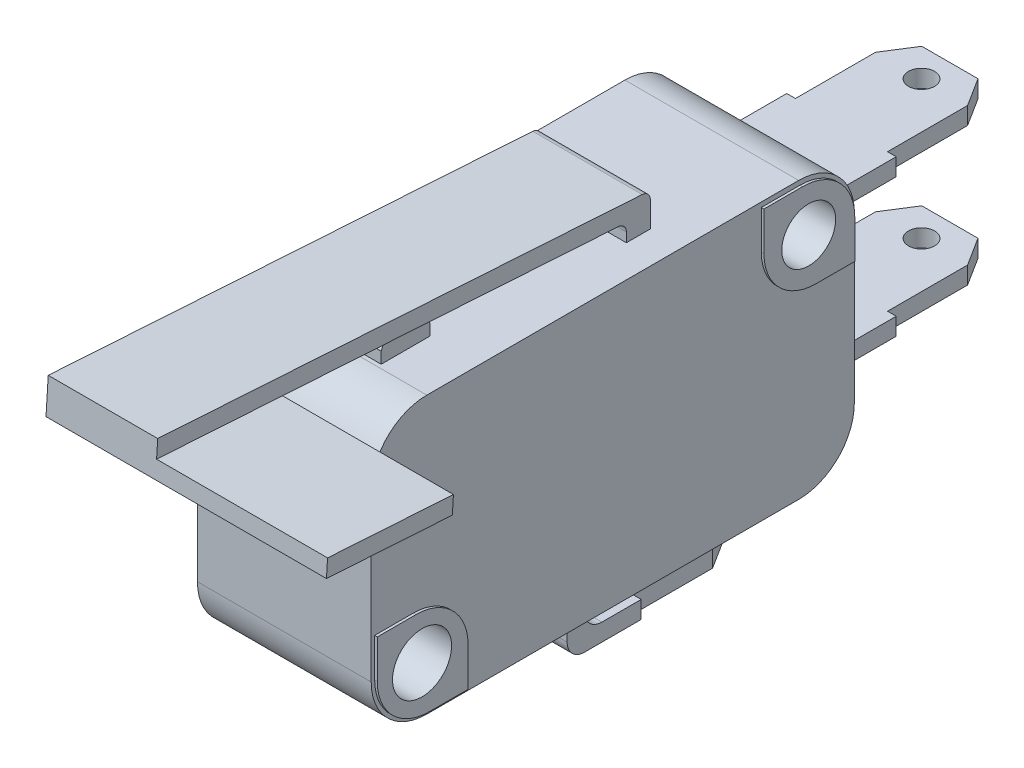
SolidWorks part; units mm, degrees
ref_plane "Plano frontal" through (0, 0, 0) normal (0, 0, 1) x (1, 0, 0)
ref_plane "Plano superior" through (0, 0, 0) normal (0, 1, 0) x (1, 0, 0)
ref_plane "Plano direito" through (0, 0, 0) normal (1, 0, 0) x (0, 0, -1)
sketch "skBlocoBase" plane through (0, 0, 0) normal (1, 0, 0) x (0, 0, -1)
  line L1 (-10.7, 7.95) -> (10.7, 7.95)
  line L2 (-13.9, 4.75) -> (-13.9, -4.75)
  line L3 (-10.7, -7.95) -> (10.7, -7.95)
  line L4 (13.9, 4.75) -> (13.9, -4.75)
  line L5 (-13.9, 7.95) -> (13.9, -7.95) construction
  line L6 (-13.9, -7.95) -> (13.9, 7.95) construction
  arc A0 (-13.9, -4.75) -> (-10.7, -7.95) centre (-10.7, -4.75) ccw
  arc A1 (10.7, -7.95) -> (13.9, -4.75) centre (10.7, -4.75) ccw
  arc A2 (10.7, 7.95) -> (13.9, 4.75) centre (10.7, 4.75) cw
  arc A3 (-10.7, 7.95) -> (-13.9, 4.75) centre (-10.7, 4.75) ccw
  point P0 (0, 0)
  dimension "D3" = 3.2
  dimension "D1" = 27.8
  dimension "D2" = 15.9
extrude "BlocoBase" add sketch "skBlocoBase" along normal mid plane 10
sketch "skFixacao" plane through (0, 0, 0) normal (1, 0, 0) x (0, 0, -1)
  line L0 (-13.9, 0) -> (13.9, 0) construction
  line L1 (-13.9, 4.75) -> (-13.9, -4.75) construction
  line L2 (13.9, -4.75) -> (13.9, 4.75) construction
  circle A0 centre (-11.125, -5.1) radius 1.7
  circle A5 centre (11.125, 5.1) radius 1.55
  dimension "D1" = 3.4
  dimension "D2" = 3.1
  dimension "D3" = 5.1
  dimension "D4" = 5.1
  dimension "D5" = 11.125
  dimension "D6" = 11.125
extrude "Fixacao" cut sketch "skFixacao" against normal mid plane 10.3
sketch "skRessaltoFixacao" plane through (5, 0, 0) normal (1, 0, 0) x (0, 0, -1)
  line L0 (-11.125, -5.1) -> (-9.9229, -6.3021) construction
  line L2 (-11.125, -5.1) -> (-11.125, -6.8) construction
  line L3 (-11.475, -2.325) -> (-13.9, -2.325) construction
  line L6 (-13.9, -2.325) -> (-13.9, -4.75) construction
  line L7 (-8.275, -5.525) -> (-8.275, -7.95) construction
  line L8 (-10.7, -7.95) -> (10.7, -7.95) construction
  line L9 (-8.275, -7.95) -> (-10.7, -7.95) construction
  line L10 (-11.475, -2.525) -> (-13.7, -2.525)
  line L11 (-13.7, -2.525) -> (-13.7, -4.75)
  line L12 (-8.475, -7.75) -> (-10.7, -7.75)
  line L13 (-8.475, -5.525) -> (-8.475, -7.75)
  line L14 (-11.325, -4.6172) -> (-11.325, -6.8)
  line L15 (-11.325, -4.6172) -> (-9.7815, -6.1607)
  line L16 (10.775, -2.525) -> (8.55, -2.525) [skipped]
  line L17 (8.55, -2.525) -> (8.55, -4.75) [skipped]
  line L18 (13.775, -7.75) -> (11.55, -7.75) [skipped]
  line L19 (13.775, -5.525) -> (13.775, -7.75) [skipped]
  line L20 (10.925, -4.6172) -> (10.925, -6.8) [skipped]
  line L21 (10.925, -4.6172) -> (12.4685, -6.1607) [skipped]
  line L22 (11.125, -5.1) -> (12.3271, -6.3021) construction
  line L23 (11.125, -5.1) -> (11.125, -6.8) construction
  line L24 (10.775, -2.325) -> (8.35, -2.325) construction
  line L25 (8.35, -2.325) -> (8.35, -4.75) construction
  line L26 (13.975, -5.525) -> (13.975, -7.95) construction
  line L27 (13.975, -7.95) -> (11.55, -7.95) construction
  line L28 (10.775, 7.675) -> (8.55, 7.675)
  line L29 (8.55, 7.675) -> (8.55, 5.45)
  line L30 (13.775, 2.45) -> (11.55, 2.45)
  line L31 (13.775, 4.675) -> (13.775, 2.45)
  line L32 (10.925, 5.5828) -> (10.925, 3.4)
  line L33 (10.925, 5.5828) -> (12.4685, 4.0393)
  line L34 (11.125, 5.1) -> (12.3271, 3.8979) construction
  line L35 (11.125, 5.1) -> (11.125, 3.4) construction
  line L36 (10.775, 7.875) -> (8.35, 7.875) construction
  line L37 (8.35, 7.875) -> (8.35, 5.45) construction
  line L38 (13.975, 4.675) -> (13.975, 2.25) construction
  line L39 (13.975, 2.25) -> (11.55, 2.25) construction
  line L40 (-11.475, 7.675) -> (-13.7, 7.675) [skipped]
  line L41 (-13.7, 7.675) -> (-13.7, 5.45) [skipped]
  line L42 (-8.475, 2.45) -> (-10.7, 2.45) [skipped]
  line L43 (-8.475, 4.675) -> (-8.475, 2.45) [skipped]
  line L44 (-11.325, 5.5828) -> (-11.325, 3.4) [skipped]
  line L45 (-11.325, 5.5828) -> (-9.7815, 4.0393) [skipped]
  line L46 (-11.125, 5.1) -> (-9.9229, 3.8979) construction
  line L47 (-11.125, 5.1) -> (-11.125, 3.4) construction
  line L48 (-11.475, 7.875) -> (-13.9, 7.875) construction
  line L49 (-13.9, 7.875) -> (-13.9, 5.45) construction
  line L50 (-8.275, 4.675) -> (-8.275, 2.25) construction
  line L51 (-8.275, 2.25) -> (-10.7, 2.25) construction
  arc A0 (-13.9, -4.75) -> (-10.7, -7.95) centre (-10.7, -4.75) ccw construction
  arc A1 (-13.9, -4.75) -> (-10.7, -7.95) centre (-10.7, -4.75) ccw construction
  arc A2 (-11.475, -2.325) -> (-8.275, -5.525) centre (-11.475, -5.525) cw construction
  circle A3 centre (-11.125, -5.1) radius 1.7 construction
  circle A4 centre (-11.125, -5.1) radius 1.7
  arc A7 (-13.7, -4.75) -> (-10.7, -7.75) centre (-10.7, -4.75) ccw
  arc A8 (-11.475, -2.525) -> (-8.475, -5.525) centre (-11.475, -5.525) cw
  circle A9 centre (11.125, -5.1) radius 1.7 [skipped]
  arc A10 (8.55, -4.75) -> (11.55, -7.75) centre (11.55, -4.75) ccw [skipped]
  arc A11 (10.775, -2.525) -> (13.775, -5.525) centre (10.775, -5.525) cw [skipped]
  arc A12 (8.35, -4.75) -> (11.55, -7.95) centre (11.55, -4.75) ccw construction
  arc A13 (10.775, -2.325) -> (13.975, -5.525) centre (10.775, -5.525) cw construction
  circle A14 centre (11.125, 5.1) radius 1.7 construction
  arc A15 (8.55, 5.45) -> (11.55, 2.45) centre (11.55, 5.45) ccw
  arc A16 (10.775, 7.675) -> (13.775, 4.675) centre (10.775, 4.675) cw
  arc A17 (8.35, 5.45) -> (11.55, 2.25) centre (11.55, 5.45) ccw construction
  arc A18 (10.775, 7.875) -> (13.975, 4.675) centre (10.775, 4.675) cw construction
  circle A19 centre (-11.125, 5.1) radius 1.7 [skipped]
  arc A20 (-13.7, 5.45) -> (-10.7, 2.45) centre (-10.7, 5.45) ccw [skipped]
  arc A21 (-11.475, 7.675) -> (-8.475, 4.675) centre (-11.475, 4.675) cw [skipped]
  arc A22 (-13.9, 5.45) -> (-10.7, 2.25) centre (-10.7, 5.45) ccw construction
  arc A23 (-11.475, 7.875) -> (-8.275, 4.675) centre (-11.475, 4.675) cw construction
  circle A24 centre (11.125, 5.1) radius 1.55 construction
  circle A25 centre (11.125, 5.1) radius 1.55
  dimension "D1" = 45
  dimension "D2" = 0.2
  dimension "D3" = 2
  dimension "D4" = 2
extrude "RessaltoFixacao" add sketch "skRessaltoFixacao" along normal blind 0.15
mirror "MirrorRessaltoFixacao" about plane through (0, 0, 0) normal (1, 0, 0) of "RessaltoFixacao"
sketch "skBotao" plane through (0, 0, 0) normal (1, 0, 0) x (0, 0, -1)
  line L0 (-9.075, 9.6) -> (-9.075, -7.95) construction
  line L1 (-10.7, -7.95) -> (10.7, -7.95) construction
  line L2 (-10.475, 7.95) -> (-10.475, 8.6)
  line L3 (10.7, 7.95) -> (-10.7, 7.95) construction
  line L4 (-7.675, 7.95) -> (-7.675, 8.6)
  line L5 (-10.475, 7.95) -> (-7.675, 7.95)
  circle A0 centre (-11.125, -5.1) radius 1.7 construction
  circle A1 centre (11.125, 5.1) radius 1.55 construction
  circle A2 centre (-11.125, -5.1) radius 1.7 construction
  circle A3 centre (11.125, 5.1) radius 1.55 construction
  arc A4 (-10.475, 8.6) -> (-7.675, 8.6) centre (-9.075, 8.12) cw
  point P6 (-9.075, 9.6)
  dimension "D3" = 1.4
  dimension "D1" = 20.2
  dimension "D2" = 14.7
  dimension "D4" = 1
extrude "Botao" add sketch "skBotao" along normal mid plane 4.3
sketch "Sketch5" plane through (0, 0, -13.9) normal (0, 0, -1) x (-1, 0, 0)
  line L0 (-5, 7.95) -> (5, 7.95) construction
  line L1 (-5, 7.95) -> (5, 7.95) construction
  line L2 (-5, 0) -> (5, 0) construction
  line L3 (-5, -4.75) -> (-5, 4.75) construction
  line L4 (5, -4.75) -> (5, 4.75) construction
  line L5 (-5, -7.95) -> (5, -7.95) construction
  line L6 (-5, 3.975) -> (5, 3.975) construction
  line L9 (-5, -3.975) -> (5, -3.975) construction
  line L10 (3.15, -4.475) -> (3.15, -3.475)
  line L11 (-3.15, 4.475) -> (3.15, 4.475)
  line L12 (-3.15, 4.475) -> (-3.15, 3.475)
  line L13 (-3.15, 3.475) -> (3.15, 3.475)
  line L14 (3.15, 4.475) -> (3.15, 3.475)
  line L15 (-3.15, 4.475) -> (3.15, 3.475) construction
  line L16 (-3.15, 3.475) -> (3.15, 4.475) construction
  line L17 (-3.15, -3.475) -> (3.15, -3.475)
  line L18 (-3.15, -4.475) -> (-3.15, -3.475)
  line L19 (-3.15, -4.475) -> (3.15, -4.475)
  point P14 (0, 3.975)
  dimension "D1" = 3.975
  dimension "D2" = 1
  dimension "D3" = 6.3
extrude "BaseConectorNONC" add sketch "Sketch5" along normal blind 10.5
sketch "skDesenhoConectorNONC" plane through (0, -4.475, 0) normal (0, -1, 0) x (1, 0, 0)
  line L0 (0, -24.4) -> (0, -13.9) construction
  line L1 (3.15, -24.4) -> (-3.15, -24.4) construction
  line L2 (3.15, -13.9) -> (-3.15, -13.9) construction
  line L3 (1.617, -24.4) -> (-1.617, -24.4)
  line L4 (3.15, -13.9) -> (-3.15, -13.9)
  line L5 (-3.15, -13.9) -> (-3.15, -18.1612)
  line L6 (-3.15, -24.4) -> (-3.15, -13.9) construction
  line L7 (-3.15, -18.1612) -> (-2.65, -18.1612)
  line L8 (-2.65, -18.1612) -> (-2.65, -22.7671)
  line L9 (-2.65, -22.7671) -> (-1.617, -24.4)
  line L10 (2.65, -22.7671) -> (1.617, -24.4)
  line L11 (2.65, -18.1612) -> (2.65, -22.7671)
  line L12 (3.15, -18.1612) -> (2.65, -18.1612)
  line L13 (3.15, -13.9) -> (3.15, -18.1612)
  line L14 (-3.15, -18.1612) -> (-3.15, -24.4)
  line L15 (-3.15, -24.4) -> (-1.617, -24.4)
  line L16 (1.617, -24.4) -> (3.15, -24.4)
  line L17 (3.15, -24.4) -> (3.15, -18.1612)
  circle A0 centre (0, -22.7671) radius 0.75
  line M2 (-3.15, -13.9) -> (-3.15, -24.4)
  line M3 (-3.15, -24.4) -> (3.15, -24.4)
  line M4 (3.15, -24.4) -> (3.15, -13.9)
  dimension "D1" = 0.5
extrude "DesenhoConectorNONC" cut sketch "skDesenhoConectorNONC" against normal blind 20.5 contours L12 L11 L10 M4 M3 | L9 L8 L7 M2 M3 | A0 L0 | L0 A0
sketch "skBaseConectorCOM" plane through (0, 0, 0) normal (1, 0, 0) x (0, 0, -1)
  line L0 (10.7, 7.95) -> (-10.7, 7.95) construction
  line L1 (9.725, -11.25) -> (0.225, -11.25)
  line L2 (-0.775, -10.25) -> (-0.775, -7.95)
  line L3 (-10.7, -7.95) -> (10.7, -7.95) construction
  line L4 (9.725, -10.25) -> (1.225, -10.25)
  line L5 (0.225, -9.25) -> (0.225, -7.95)
  line L6 (9.725, -10.25) -> (9.725, -11.25)
  line L7 (0.225, -7.95) -> (-0.775, -7.95)
  circle A0 centre (-11.125, -5.1) radius 1.7 construction
  circle A1 centre (11.125, 5.1) radius 1.55 construction
  circle A2 centre (-11.125, -5.1) radius 1.7 construction
  circle A3 centre (11.125, 5.1) radius 1.55 construction
  arc A4 (1.225, -10.25) -> (0.225, -9.25) centre (1.225, -9.25) cw
  arc A5 (0.225, -11.25) -> (-0.775, -10.25) centre (0.225, -10.25) cw
  point P6 (9.725, -11.25)
  point P22 (-0.775, -11.25)
  dimension "D5" = 1
  dimension "D1" = 19.2
  dimension "D2" = 1.4
  dimension "D3" = 10.5
  dimension "D4" = 1
extrude "BaseConectorCOM" add sketch "skBaseConectorCOM" along normal mid plane 6.3
sketch "skDesenhoConectorCOM" plane through (0, -11.25, 0) normal (0, -1, 0) x (1, 0, 0)
  line L0 (0, -9.725) -> (0, 0.775) construction
  line L1 (1.617, -9.725) -> (-1.617, -9.725)
  line L2 (3.15, 0.775) -> (-3.15, 0.775)
  line L3 (-3.15, 0.775) -> (-3.15, -3.4862)
  line L4 (-3.15, -3.4862) -> (-2.65, -3.4862)
  line L5 (-2.65, -3.4862) -> (-2.65, -8.0921)
  line L6 (-2.65, -8.0921) -> (-1.617, -9.725)
  line L7 (2.65, -8.0921) -> (1.617, -9.725)
  line L8 (2.65, -3.4862) -> (2.65, -8.0921)
  line L9 (3.15, -3.4862) -> (2.65, -3.4862)
  line L10 (3.15, 0.775) -> (3.15, -3.4862)
  line L11 (-3.15, -3.4862) -> (-3.15, -9.725)
  line L12 (-3.15, -9.725) -> (-1.617, -9.725)
  line L13 (1.617, -9.725) -> (3.15, -9.725)
  line L14 (3.15, -9.725) -> (3.15, -3.4862)
  circle A0 centre (0, -8.0921) radius 0.75
  line M1 (-3.15, -0.225) -> (-3.15, -9.725)
  line M2 (-3.15, -9.725) -> (3.15, -9.725)
  line M3 (3.15, -9.725) -> (3.15, -0.225)
  dimension "D1" = 0.5
extrude "DesenhoConectorCOM" cut sketch "skDesenhoConectorCOM" against normal up to surface (1 mm away) contours L9 L8 L7 M3 M2 | L0 A0 | A0 L0 | L6 L5 L4 M1 M2
sketch "skBaseContato" plane through (0, 0, 0) normal (1, 0, 0) x (0, 0, -1)
  line L0 (2.633, 7.95) -> (2.633, 8.4866)
  line L1 (10.7, 7.95) -> (-10.7, 7.95) construction
  line L2 (2.1649, 8.9856) -> (-24.4, 10.6816)
  line L3 (-24.4, 10.6816) -> (-24.3363, 11.6796)
  line L4 (-24.3363, 11.6796) -> (3.5456, 9.8995)
  line L5 (4.0137, 9.4005) -> (4.0137, 7.95)
  line L6 (4.0137, 7.95) -> (2.633, 7.95)
  line L7 (-13.9, 4.75) -> (-13.9, -4.75) construction
  arc A0 (-7.675, 8.6) -> (-10.475, 8.6) centre (-9.075, 8.12) ccw construction
  arc A1 (-7.675, 8.6) -> (-10.475, 8.6) centre (-9.075, 8.12) ccw construction
  arc A2 (3.5456, 9.8995) -> (4.0137, 9.4005) centre (3.5137, 9.4005) cw
  arc A3 (2.633, 8.4866) -> (2.1649, 8.9856) centre (2.133, 8.4866) ccw
  dimension "D4" = 0.5
  dimension "D1" = 1
  dimension "D2" = 0.1
  dimension "D3" = 10.5
extrude "BaseContato" add sketch "skBaseContato" along normal mid plane 6.3
sketch "skApoioRolo" plane through (3.15, 0, 0) normal (1, 0, 0) x (0, 0, -1)
  line L0 (-22.9391, 11.5904) -> (-22.6936, 15.4355) construction
  line L1 (3.5456, 9.8995) -> (-24.3363, 11.6796) construction
  line L2 (-24.3363, 11.6796) -> (-24.4, 10.6816) construction
  line L3 (-24.1542, 14.4868) -> (-24.3363, 11.6796)
  line L4 (-24.3363, 11.6796) -> (-22.9391, 11.5904)
  line L5 (-22.9391, 11.5904) -> (-21.542, 11.5012)
  line L6 (-21.542, 11.5012) -> (-21.3542, 14.4868)
  arc A0 (-21.3652, 14.3114) -> (-24.1542, 14.4868) centre (-22.7542, 14.4868) ccw
  circle A1 centre (-22.7542, 14.4868) radius 0.7
  dimension "D1" = 1.4
extrude "ApoioRolo" add sketch "skApoioRolo" against normal blind 1
mirror "MirrorApoioRolo" about plane through (0, 0, 0) normal (1, 0, 0) of "ApoioRolo"
sketch "skRolo" plane through (2.15, 0, 0) normal (-1, 0, 0) x (0, 0, 1)
  circle A0 centre (22.7542, 14.4868) radius 2.5
extrude "Rolo" add sketch "skRolo" along normal offset from surface (4.3 mm away) 1 up to face at (-3.15, 10.6449, 8.7805)
sketch "Sketch6" plane through (0, 10.0848, -0.6439) normal (0, 0.998, -0.0637) x (1, 0, 0)
  line L0 (3.15, 2.9076) -> (3.15, -22.231) construction
  line L1 (3.15, -18.247) -> (-11.8877, -18.247)
  line L2 (3.15, -18.247) -> (3.15, -29.0953)
  line L3 (3.15, -29.0953) -> (-11.8877, -29.0953)
  line L4 (-11.8877, -18.247) -> (-11.8877, -29.0953)
extrude "Cut-Extrude1" cut sketch "Sketch6" along normal blind 10
sketch "Sketch7" plane through (0, 9.0868, -0.5801) normal (0, -0.998, 0.0637) x (1, 0, 0)
  line L1 (-3.15, 25.031) -> (12.9877, 25.031)
  line L2 (-3.15, 25.031) -> (-3.15, 17.772)
  line L3 (-3.15, 17.772) -> (12.9877, 17.772)
  line L4 (12.9877, 25.031) -> (12.9877, 17.772)
extrude "Boss-Extrude1" add sketch "Sketch7" along normal blind 1
